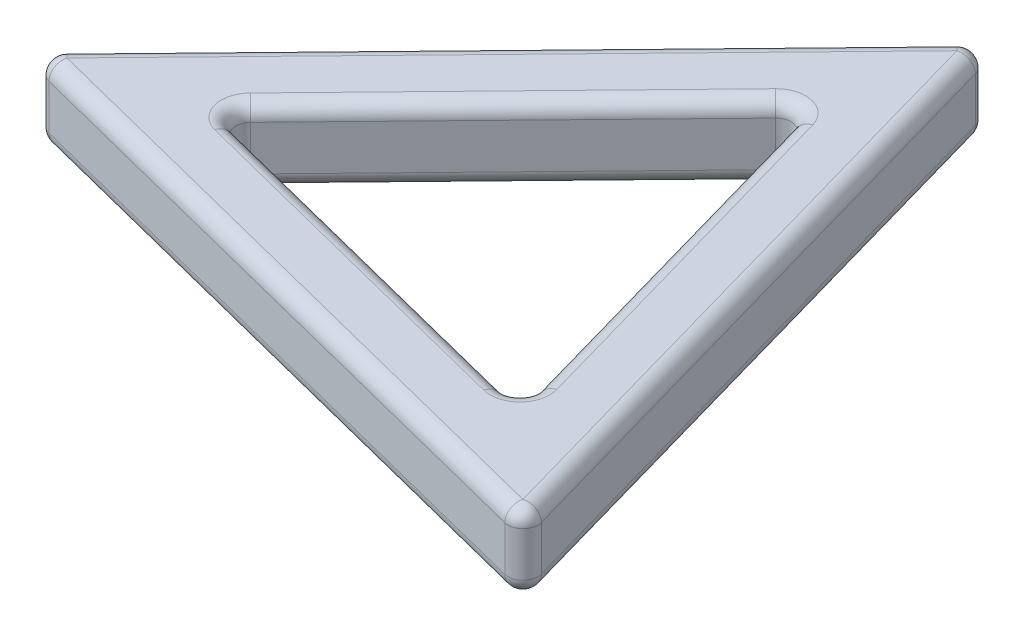
SolidWorks part; units mm, degrees
ref_plane "Front Plane" through (0, 0, 0) normal (0, 0, 1) x (1, 0, 0)
ref_plane "Top Plane" through (0, 0, 0) normal (0, 1, 0) x (1, 0, 0)
ref_plane "Right Plane" through (0, 0, 0) normal (1, 0, 0) x (0, 0, -1)
sketch "Sketch1" plane through (0, 0, 0) normal (0, 1, 0) x (1, 0, 0)
  line L0 (23.4984, -22.8402) -> (8.031, 31.7703)
  line L1 (-31.5294, -8.9301) -> (23.4984, -22.8402)
  line L2 (8.031, 31.7703) -> (-31.5294, -8.9301)
  line L9 (37.84, -36.78) -> (12.9325, 51.1604)
  line L10 (12.9325, 51.1604) -> (-50.7724, -14.3804)
  line L11 (-50.7724, -14.3804) -> (37.84, -36.78)
  dimension "D1" = 10
extrude "Extrude1" add sketch "Sketch1" along normal blind 10
fillet "Fillet1" radius 2 18 edges at (-4.0155, 0, 15.8852) (15.7647, 0, -4.4651) (-11.7492, 0, -11.4201) (-4.0155, 10, 15.8852) (15.7647, 10, -4.4651) (-11.7492, 10, -11.4201) (-31.5294, 5, 8.9301) (8.031, 5, -31.7703) (23.4984, 5, 22.8402) (-6.4662, 0, 25.5802) (25.3862, 0, -7.1902) (-18.92, 0, -18.39) (-6.4662, 10, 25.5802) (25.3862, 10, -7.1902) (-18.92, 10, -18.39) (-50.7724, 5, 14.3804) (12.9325, 5, -51.1604) (37.84, 5, 36.78)
